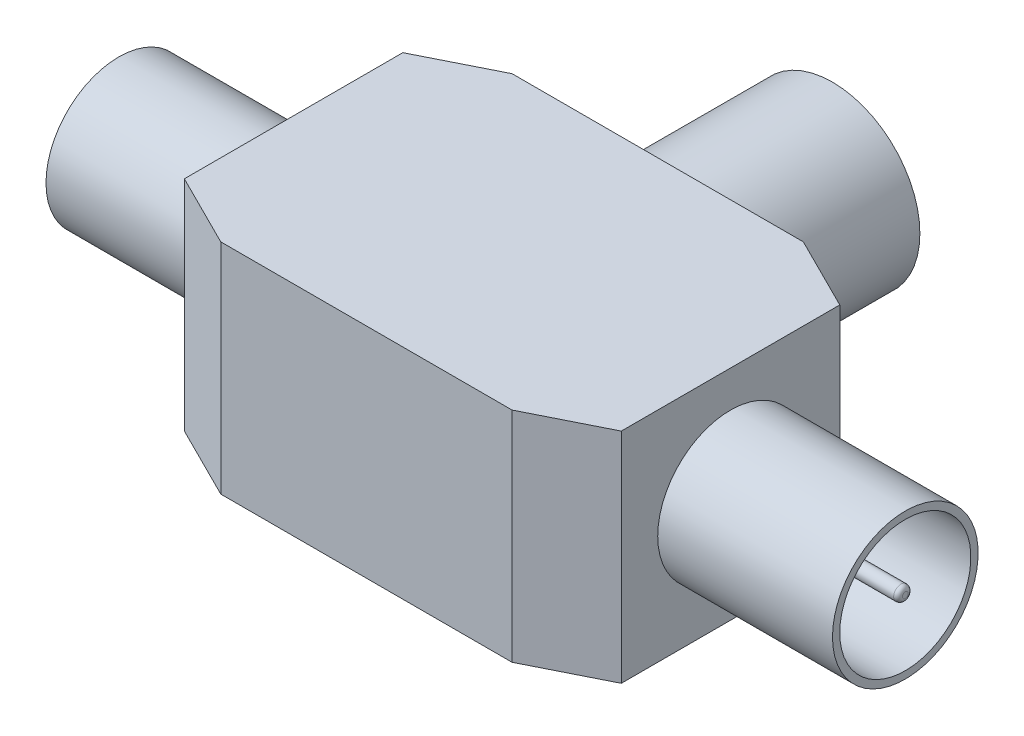
SolidWorks part; units mm, degrees
ref_plane "Front Plane" through (0, 0, 0) normal (0, 0, 1) x (1, 0, 0)
ref_plane "Top Plane" through (0, 0, 0) normal (0, 1, 0) x (1, 0, 0)
ref_plane "Right Plane" through (0, 0, 0) normal (1, 0, 0) x (0, 0, -1)
sketch "Sketch1" plane through (0, 0, 0) normal (0, 1, 0) x (1, 0, 0)
  line L0 (10, 20) -> (15, 17.5)
  line L1 (-10, 0) -> (10, 0)
  line L2 (-15, 2.5) -> (-15, 17.5)
  line L3 (-10, 20) -> (10, 20)
  line L4 (15, 2.5) -> (15, 17.5)
  line L5 (10, 0) -> (15, 2.5)
  line L6 (-15, 17.5) -> (-10, 20)
  line L7 (-15, 2.5) -> (-10, 0)
  point P0 (-15, 0)
  point P1 (15, 20)
  point P2 (-15, 20)
  point P3 (15, 0)
  dimension "D1" = 30
  dimension "D2" = 20
  dimension "D3" = 5
  dimension "D4" = 2.5
  dimension "D5" = 5
  dimension "D6" = 2.5
  dimension "D7" = 5
  dimension "D8" = 2.5
  dimension "D9" = 5
  dimension "D10" = 2.5
extrude "Boss-Extrude1" add sketch "Sketch1" along normal blind 15
sketch "Sketch2" plane through (0, 0, -20) normal (0, 0, -1) x (-1, 0, 0)
  line L0 (-10, 7.5) -> (10, 7.5) construction
  line L1 (-10, 15) -> (-10, 0) construction
  line L2 (10, 15) -> (10, 0) construction
  circle A0 centre (0, 7.5) radius 6
  circle A1 centre (0, 7.5) radius 5.5
  point P10 (0, 7.5)
  point P12 (0, 0)
  dimension "D1" = 12
  dimension "D2" = 0.5
extrude "Boss-Extrude2" add sketch "Sketch2" along normal blind 12
sketch "Sketch3" plane through (0, 0, -20) normal (0, 0, -1) x (-1, 0, 0)
  circle A0 centre (0, 7.5) radius 1
  circle A1 centre (0, 7.5) radius 0.8
  dimension "D1" = 2
  dimension "D2" = 0.2
extrude "Boss-Extrude3" add sketch "Sketch3" along normal blind 12
sketch "Sketch4" plane through (-15, 0, 0) normal (-1, 0, 0) x (0, 0, 1)
  line L0 (-17.5, 7.5) -> (-2.5, 7.5) construction
  line L1 (-17.5, 15) -> (-17.5, 0) construction
  line L2 (-2.5, 15) -> (-2.5, 0) construction
  circle A0 centre (-10, 7.5) radius 5
  circle A1 centre (-10, 7.5) radius 4.5
  circle A2 centre (-10, 7.5) radius 0.5
  dimension "D1" = 10
  dimension "D3" = 1
  dimension "D2" = 0.5
extrude "Boss-Extrude4" add sketch "Sketch4" along normal blind 12
fillet "Fillet2" radius 0.3 1 edges at (-27, 7.5, -9.5)
mirror "Mirror1" about plane through (0, 0, 0) normal (1, 0, 0) of "Fillet2", "Boss-Extrude4"
